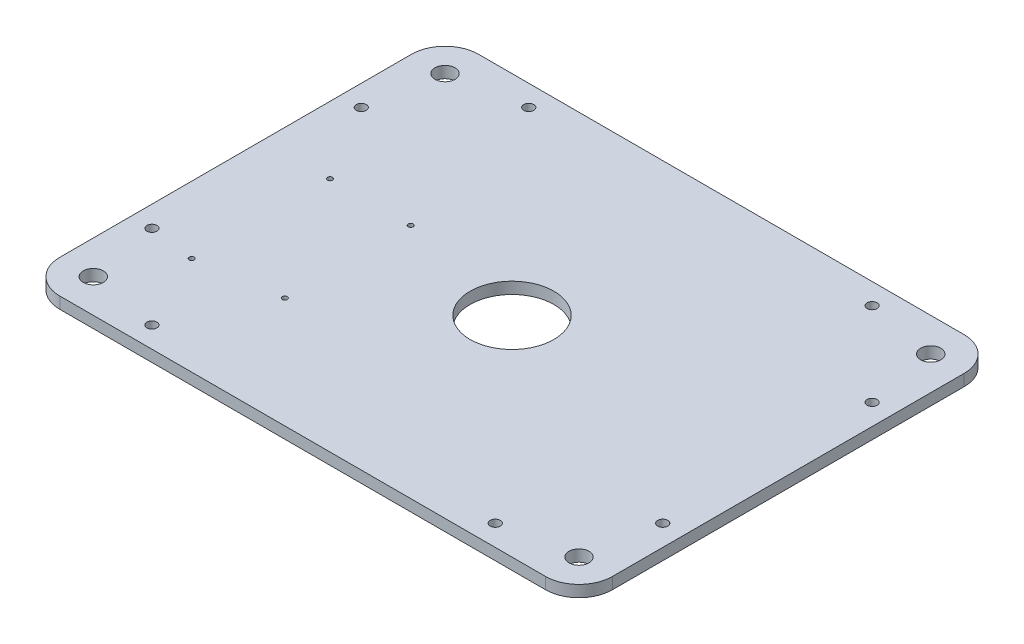
SolidWorks part; units mm, degrees
material "Delrin 2700 NC010, Low Viscosity Acetal Copolymer (SS)"
ref_plane "Front Plane" through (0, 0, 0) normal (0, 0, 1) x (1, 0, 0)
ref_plane "Top Plane" through (0, 0, 0) normal (0, 1, 0) x (1, 0, 0)
ref_plane "Right Plane" through (0, 0, 0) normal (1, 0, 0) x (0, 0, -1)
sketch "Sketch1" plane through (0, 0, 0) normal (0, 1, 0) x (1, 0, 0)
  line L0 (165, 125) -> (-165, -125) construction
  line L5 (-165, -125) -> (165, -125)
  line L6 (-165, -125) -> (-165, 125)
  line L7 (-165, 125) -> (165, 125)
  line L8 (165, -125) -> (165, 125)
  point P5 (0, 0)
  dimension "D1" = 330
  dimension "D2" = 250
extrude "Boss-Extrude1" add sketch "Sketch1" along normal blind 6.9
sketch "Sketch2" plane through (0, 6.9, 0) normal (0, 1, 0) x (1, 0, 0)
  line L0 (145, 105) -> (-145, -105) construction
  line L1 (-145, 105) -> (145, 105) construction
  line L2 (-145, 105) -> (-145, -105) construction
  line L3 (-145, -105) -> (145, -105) construction
  line L4 (145, 105) -> (145, -105) construction
  line L5 (0, 105) -> (0, 125) construction
  line L6 (165, 125) -> (-165, 125) construction
  line L8 (-145, 0) -> (-165, 0) construction
  line L9 (-165, 125) -> (-165, -125) construction
  circle A0 centre (-145, 105) radius 6
  circle A1 centre (145, 105) radius 6
  circle A2 centre (145, -105) radius 6
  circle A3 centre (-145, -105) radius 6
  point P4 (0, 0)
  dimension "D2" = 12
  dimension "D1" = 20
extrude "Cut-Extrude1" cut sketch "Sketch2" against normal through all
sketch "Sketch3" plane through (0, 6.9, 0) normal (0, 1, 0) x (1, 0, 0)
  circle A0 centre (0, 0) radius 25
  dimension "D1" = 50
extrude "Cut-Extrude2" cut sketch "Sketch3" against normal through all
sketch "Sketch4" plane through (0, 6.9, 0) normal (0, 1, 0) x (1, 0, 0)
  line L0 (-152.5, -62.5) -> (-152.5, -112.5) construction
  line L1 (-152.5, -112.5) -> (-102.5, -112.5) construction
  line L2 (-102.5, -112.5) -> (-152.5, -62.5) construction
  line L3 (-165, 0) -> (165, 0) construction
  line L4 (-165, 125) -> (-165, -125) construction
  line L5 (165, -125) -> (165, 125) construction
  line L6 (165, 0) -> (0, 125) construction
  line L7 (165, 125) -> (-165, 125) construction
  line L8 (0, 125) -> (0, -125) construction
  line L9 (-165, -125) -> (165, -125) construction
  line L10 (-102.5, 112.5) -> (-152.5, 62.5) construction
  line L11 (-152.5, 112.5) -> (-102.5, 112.5) construction
  line L12 (-152.5, 62.5) -> (-152.5, 112.5) construction
  line L13 (152.5, 62.5) -> (152.5, 112.5) construction
  line L14 (152.5, 112.5) -> (102.5, 112.5) construction
  line L15 (102.5, 112.5) -> (152.5, 62.5) construction
  line L16 (102.5, -112.5) -> (152.5, -62.5) construction
  line L17 (152.5, -112.5) -> (102.5, -112.5) construction
  line L18 (152.5, -62.5) -> (152.5, -112.5) construction
  line L19 (-165, -125) -> (-152.5, -112.5) construction
  line L20 (-152.5, -112.5) -> (-127.5, -87.5) construction
  circle A0 centre (-152.5, -62.5) radius 3
  circle A1 centre (-102.5, -112.5) radius 3
  circle A2 centre (-102.5, 112.5) radius 3
  circle A3 centre (-152.5, 62.5) radius 3
  circle A4 centre (152.5, 62.5) radius 3
  circle A5 centre (102.5, 112.5) radius 3
  circle A6 centre (102.5, -112.5) radius 3
  circle A7 centre (152.5, -62.5) radius 3
  dimension "D2" = 6
  dimension "D1" = 50
  dimension "D3" = 12.5
extrude "Cut-Extrude3" cut sketch "Sketch4" against normal through all
fillet "Fillet1" radius 20 4 edges at (165, 3.45, -125) (-165, 3.45, -125) (-165, 3.45, 125) (165, 3.45, 125)
sketch "Sketch5" plane through (0, 6.9, 0) normal (0, 1, 0) x (1, 0, 0)
  line L0 (-125, 16.275) -> (-125, -66.275) construction
  line L1 (-165, 105) -> (-165, -105) construction
  line L2 (-125, -25) -> (-165, -25) construction
  line L3 (-165, 0) -> (165, 0) construction
  line L4 (165, -105) -> (165, 105) construction
  line L5 (-76.74, 16.275) -> (-76.74, -58.909) construction
  line L6 (-125, 16.275) -> (-76.74, 16.275) construction
  circle A0 centre (-125, 16.275) radius 1.5
  circle A1 centre (-76.74, 16.275) radius 1.5
  circle A2 centre (-125, -66.275) radius 1.5
  circle A3 centre (-76.74, -58.909) radius 1.5
  dimension "D6" = 3
  dimension "D1" = 82.55
  dimension "D2" = 40
  dimension "D3" = 25
  dimension "D4" = 75.184
  dimension "D5" = 48.26
extrude "Cut-Extrude4" cut sketch "Sketch5" against normal through all
